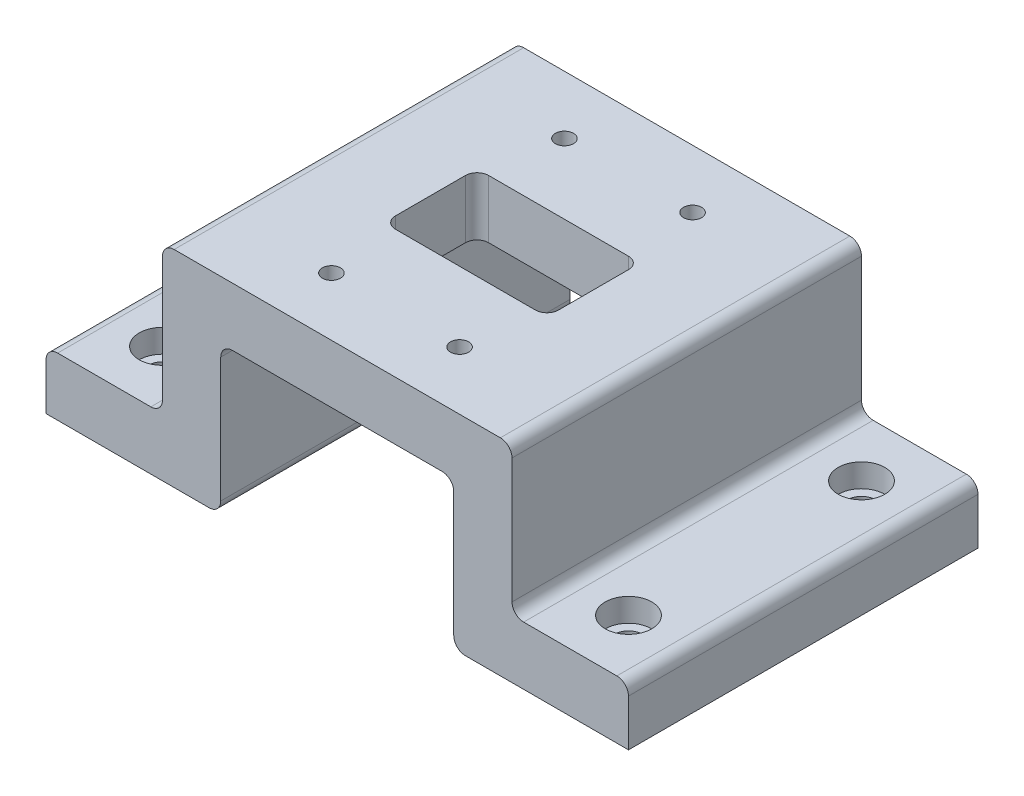
SolidWorks part; units mm, degrees
ref_plane "Front Plane" through (0, 0, 0) normal (0, 0, 1) x (1, 0, 0)
ref_plane "Top Plane" through (0, 0, 0) normal (0, 1, 0) x (1, 0, 0)
ref_plane "Right Plane" through (0, 0, 0) normal (1, 0, 0) x (0, 0, -1)
sketch "Sketch2" plane through (0, 0, 0) normal (0, 1, 0) x (1, 0, 0)
  line L0 (-30, 30) -> (30, 30)
  line L1 (-30, 30) -> (-30, -30)
  line L2 (30, 30) -> (30, -30)
  line L3 (-30, -30) -> (30, -30)
  line L4 (30, -30) -> (-30, 30) construction
  point P0 (0, 0)
  dimension "D1" = 60
  dimension "D2" = 60
extrude "Boss-Extrude1" add sketch "Sketch2" along normal blind 10
sketch "Sketch7" plane through (0, 10, 0) normal (0, 1, 0) x (1, 0, 0)
  line L0 (-14, 8) -> (14, 8)
  line L1 (-14, 8) -> (-14, -8)
  line L2 (14, 8) -> (14, -8)
  line L3 (-14, -8) -> (14, -8)
  line L4 (14, -8) -> (-14, 8) construction
  point P0 (0, 0)
  dimension "D1" = 28
  dimension "D2" = 16
extrude "Cut-Extrude2" cut sketch "Sketch7" against normal through all
fillet "Fillet2" radius 2 4 edges at (-14, 5, 8) (14, 5, 8) (14, 5, -8) (-14, 5, -8)
hole_wizard "CBORE for M2.5 SHCS2" positions "Sketch9" profile "Sketch10" counterbore size "M2.5" standard "ANSI Metric" end condition up to next
sketch "Sketch9" plane through (0, 0, 0) normal (0, -1, 0) x (-1, 0, 0)
  line L0 (-11, 20) -> (11, 20) construction
  line L1 (-11, 20) -> (-11, -20) construction
  line L2 (11, 20) -> (11, -20) construction
  line L3 (-11, -20) -> (11, -20) construction
  line L4 (11, -20) -> (-11, 20) construction
  point P0 (11, -20)
  point P2 (-11, -20)
  point P4 (11, 20)
  point P6 (-11, 20)
  point P50 (0, 0)
  dimension "D1" = 22
  dimension "D2" = 40
sketch "Sketch10" plane through (-11, 0, 20) normal (1, 0, 0) x (0, 0, -1)
  line L0 (0, 0) -> (0, 10)
  line L1 (0, 10) -> (1.55, 10)
  line L3 (1.55, 10) -> (1.55, 2.5)
  line L4 (1.55, 2.5) -> (2.75, 2.5)
  line L5 (2.75, 2.5) -> (2.75, 0)
  line L7 (2.75, 0) -> (0, 0)
  line L11 (0, -6.35) -> (0, 107.95) construction
  dimension "Thru Hole Dia." = 3.1
  dimension "Thru Hole Depth" = 10
  dimension "C'Bore Dia." = 5.5
  dimension "C'Bore Depth" = 2.5
other "Move Face1" face at (11, 2.5, -21.55) face at (-11, 2.5, -21.55) face at (11, 2.5, 18.45) face at (-11, 2.5, 18.45) parameters "D1"=3.5
sketch "Sketch11" plane through (0, 0, -30) normal (0, 0, -1) x (-1, 0, 0)
  line L0 (-30, 0) -> (-20, 0)
  line L1 (-30, 0) -> (-30, -25.4)
  line L2 (-20, 0) -> (-20, -25.4)
  line L3 (-30, -25.4) -> (-20, -25.4)
  line L4 (-30, 0) -> (30, 0) construction
  line L5 (-30, 10) -> (30, 10) construction
  dimension "D1" = 10
  dimension "D2" = 35.4
extrude "Boss-Extrude2" add sketch "Sketch11" against normal up to surface (60 mm away) up to face at (0, 5, 30)
sketch "Sketch12" plane through (0, -25.4, 0) normal (0, -1, 0) x (1, 0, 0)
  line L0 (30, 30) -> (30, -30)
  line L1 (30, 30) -> (50, 30)
  line L2 (30, -30) -> (50, -30)
  line L3 (50, 30) -> (50, -30)
  dimension "D1" = 20
extrude "Boss-Extrude3" add sketch "Sketch12" against normal blind 10
hole_wizard "CBORE for M4 SHCS1" positions "Sketch13" profile "Sketch14" counterbore size "M4" standard "ANSI Metric" end condition up to next
sketch "Sketch13" plane through (0, -15.4, 0) normal (0, 1, 0) x (1, 0, 0)
  line L4 (40, 0) -> (50, 0) construction
  line L5 (50, 30) -> (50, -30) construction
  line L7 (40, 20) -> (40, -20) construction
  line L9 (50, -30) -> (30, -30) construction
  point P0 (40, 20)
  point P2 (40, -20)
  point P24 (40, 0)
  point P28 (40, -30)
  dimension "D1" = 40
sketch "Sketch14" plane through (40, -15.4, -20) normal (1, 0, 0) x (0, 0, 1)
  line L0 (0, 0) -> (0, 10.001)
  line L1 (0, 10.001) -> (2.4, 10.001)
  line L3 (2.4, 10.001) -> (2.4, 4)
  line L4 (2.4, 4) -> (4, 4)
  line L5 (4, 4) -> (4, 0)
  line L7 (4, 0) -> (0, 0)
  line L11 (0, -6.35) -> (0, 107.95) construction
  dimension "Thru Hole Dia." = 4.8
  dimension "Thru Hole Depth" = 10.001
  dimension "C'Bore Dia." = 8
  dimension "C'Bore Depth" = 4
mirror "Mirror1" about plane through (0, 0, 0) normal (1, 0, 0) of "CBORE for M4 SHCS1", "Boss-Extrude3", "Boss-Extrude2"
fillet "Fillet5" radius 2 10 edges at (30, 10, 0) (-30, 10, 0) (-20, -25.4, 0) (20, -25.4, 0) (20, 0, 0) (-20, 0, 0) (30, -15.4, 0) (-30, -15.4, 0) (-50, -15.4, 0) (50, -15.4, 0)
